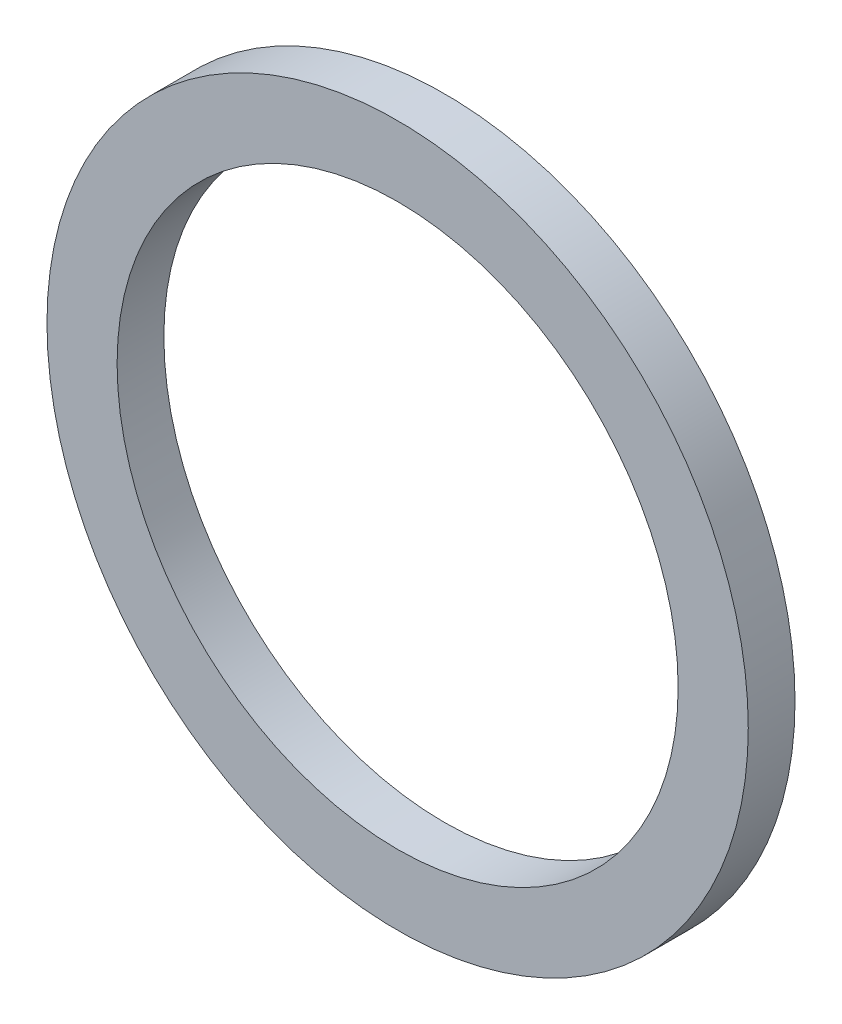
SolidWorks part; units mm, degrees
ref_plane "Plan de face" through (0, 0, 0) normal (0, 0, 1) x (1, 0, 0)
ref_plane "Plan de dessus" through (0, 0, 0) normal (0, 1, 0) x (1, 0, 0)
ref_plane "Plan de droite" through (0, 0, 0) normal (1, 0, 0) x (0, 0, -1)
sketch "Esquisse1" plane through (0, 0, 0) normal (0, 0, 1) x (1, 0, 0)
  circle A0 centre (0, 0) radius 15
  dimension "D1" = 30
extrude "Boss.-Extru.1" add sketch "Esquisse1" along normal blind 2
sketch "Esquisse2" plane through (0, 0, 2) normal (0, 0, 1) x (1, 0, 0)
  circle A0 centre (0, 0) radius 12
  dimension "D1" = 24
extrude "Enlèv. mat.-Extru.1" cut sketch "Esquisse2" against normal through all
